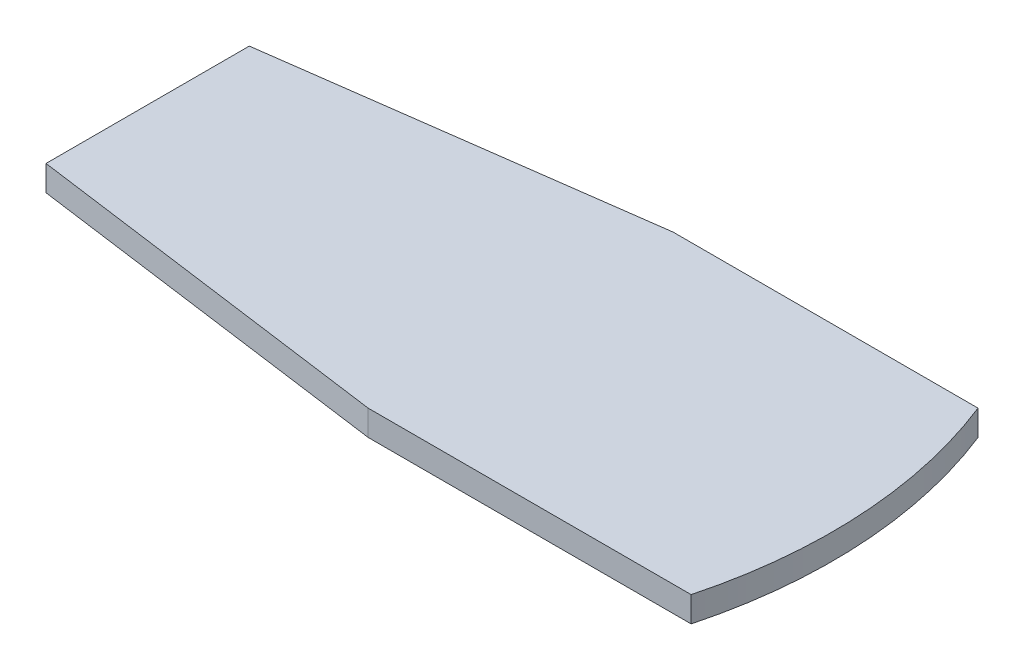
SolidWorks part; units mm, degrees
ref_plane "Front Plane" through (0, 0, 0) normal (0, 0, 1) x (1, 0, 0)
ref_plane "Top Plane" through (0, 0, 0) normal (0, 1, 0) x (1, 0, 0)
ref_plane "Right Plane" through (0, 0, 0) normal (1, 0, 0) x (0, 0, -1)
sketch "Sketch1" plane through (0, 0, 0) normal (0, 1, 0) x (1, 0, 0)
  line L0 (0, 0) -> (-88.9, 0) construction
  line L2 (-4.203, 19.05) -> (-42.303, 19.05)
  line L3 (-88.9, -12.7) -> (-88.9, 12.7)
  line L4 (-88.9, 12.7) -> (-42.303, 19.05)
  line L5 (-88.9, -12.7) -> (-42.303, -19.05)
  line L6 (-1.9455, -19.05) -> (-42.303, -19.05)
  arc A0 (-4.203, 19.05) -> (-1.9455, -19.05) centre (-60.7677, -3.4184) cw
  point P38 (-23.2638, 0)
  point P40 (-23.2638, 0)
  point P56 (-23.2638, 0)
  dimension "D1" = 38.1
  dimension "D2" = 4.203
  dimension "D3" = 12.7
  dimension "D4" = 38.1
extrude "Boss-Extrude1" add sketch "Sketch1" against normal blind 3.175
sketch "Sketch2" plane through (0, 0, 0) normal (0, 1, 0) x (1, 0, 0)
  line L0 (-23.368, 0) -> (-11.6053, 6.7912)
  line L1 (-23.368, 0) -> (-23.368, 13.5824)
  line L2 (-23.368, 10.6184) -> (-21.2127, 12.7737)
  line L3 (-23.368, 10.6184) -> (-25.5233, 12.7737)
  line L4 (-14.1722, 5.3092) -> (-11.228, 4.5203)
  line L5 (-14.1722, 5.3092) -> (-13.3833, 8.2534)
  line L6 (-23.368, 0) -> (-11.6053, -6.7912)
  line L7 (-14.1722, -5.3092) -> (-13.3833, -8.2534)
  line L8 (-14.1722, -5.3092) -> (-11.228, -4.5203)
  line L9 (-23.368, 0) -> (-23.368, -13.5824)
  line L10 (-23.368, -10.6184) -> (-25.5233, -12.7737)
  line L11 (-23.368, -10.6184) -> (-21.2127, -12.7737)
  line L12 (-23.368, 0) -> (-35.1307, -6.7912)
  line L13 (-32.5638, -5.3092) -> (-35.508, -4.5203)
  line L14 (-32.5638, -5.3092) -> (-33.3527, -8.2534)
  line L15 (-23.368, 0) -> (-35.1307, 6.7912)
  line L16 (-32.5638, 5.3092) -> (-33.3527, 8.2534)
  line L17 (-32.5638, 5.3092) -> (-35.508, 4.5203)
  arc A0 (-23.368, 6.7912) -> (-17.4866, 3.3956) centre (-15.9087, 12.9199) ccw
  arc A1 (-17.4866, 3.3956) -> (-17.4866, -3.3956) centre (-8.4494, 0) ccw
  arc A2 (-17.4866, -3.3956) -> (-23.368, -6.7912) centre (-15.9087, -12.9199) ccw
  arc A3 (-23.368, -6.7912) -> (-29.2494, -3.3956) centre (-30.8273, -12.9199) ccw
  arc A4 (-29.2494, -3.3956) -> (-29.2494, 3.3956) centre (-38.2866, 0) ccw
  arc A5 (-29.2494, 3.3956) -> (-23.368, 6.7912) centre (-30.8273, 12.9199) ccw
  point P28 (-23.368, 0)
  point P38 (-23.368, 0)
